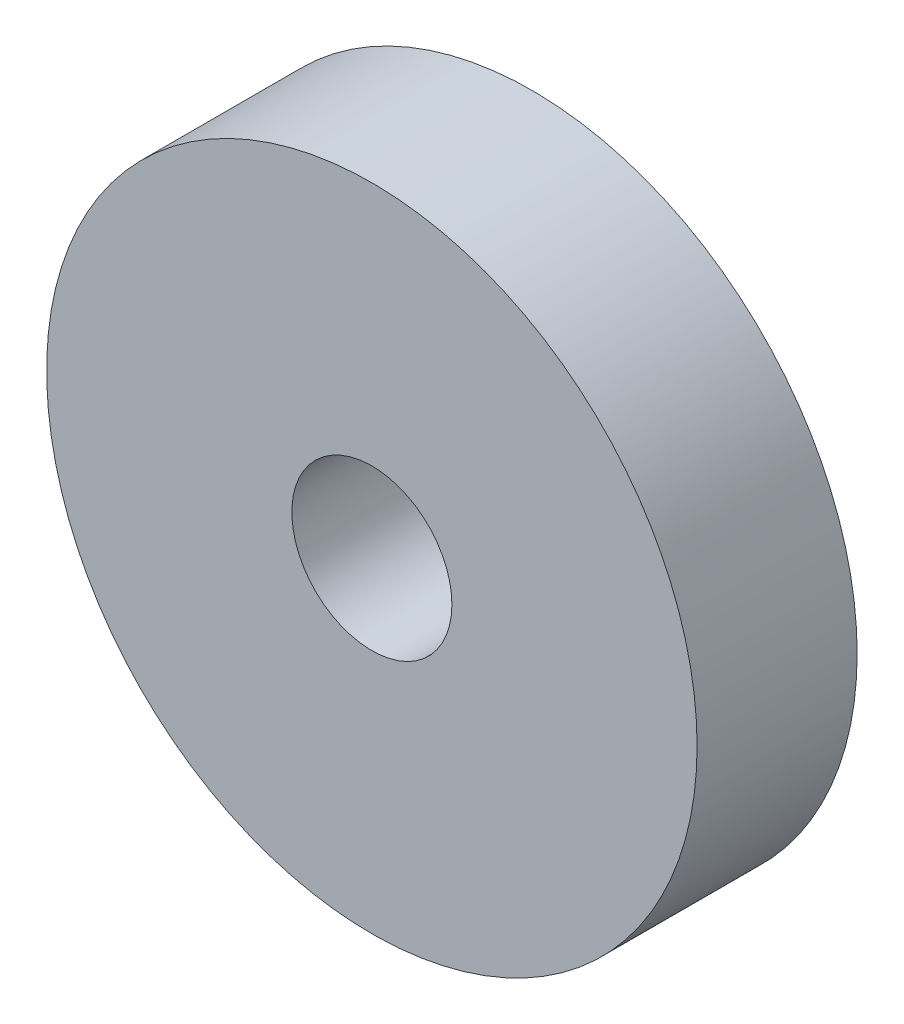
SolidWorks part; units mm, degrees
ref_plane "Front Plane" through (0, 0, 0) normal (0, 0, 1) x (1, 0, 0)
ref_plane "Top Plane" through (0, 0, 0) normal (0, 1, 0) x (1, 0, 0)
ref_plane "Right Plane" through (0, 0, 0) normal (1, 0, 0) x (0, 0, -1)
sketch "Sketch1" plane through (0, 0, 0) normal (0, 0, 1) x (1, 0, 0)
  circle A0 centre (0, 0) radius 6.35 construction
  circle A1 centre (0, 0) radius 1.5875
  circle A2 centre (0, 0) radius 6.4516
  dimension "D1" = 12.7
  dimension "D2" = 3.175
  dimension "D3" = 0.1016
extrude "Boss-Extrude1" add sketch "Sketch1" along normal blind 3.175 contours A0
equation "\"m\"= 2.28833"
